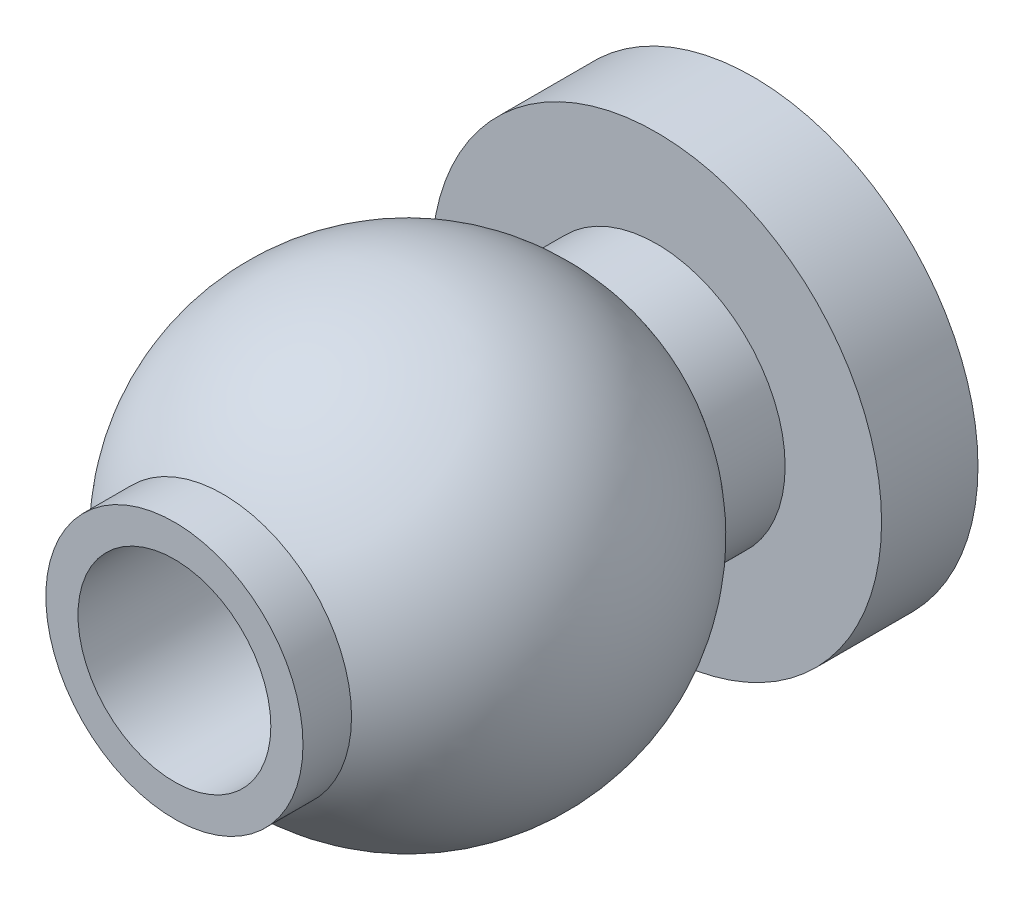
SolidWorks part; units mm, degrees
material "1060 Alloy"
ref_plane "Front Plane" through (0, 0, 0) normal (0, 0, 1) x (1, 0, 0)
ref_plane "Top Plane" through (0, 0, 0) normal (0, 1, 0) x (1, 0, 0)
ref_plane "Right Plane" through (0, 0, 0) normal (1, 0, 0) x (0, 0, -1)
sketch "Sketch1" plane through (0, 0, 0) normal (1, 0, 0) x (0, 0, -1)
  line L0 (0, 0) -> (9, 0) construction
  line L1 (0, 1.5) -> (9, 1.5)
  line L2 (9, 1.5) -> (9, 3.5)
  line L3 (9, 3.5) -> (7.5, 3.5)
  line L4 (7.5, 3.5) -> (7.5, 2)
  line L5 (7.5, 2) -> (6.5, 2)
  line L6 (0, 1.5) -> (0, 2)
  line L7 (0, 2) -> (0.7554, 2)
  arc A3 (6.5, 2) -> (0.7554, 2) centre (3.6277, 0) ccw
  dimension "D1" = 9
  dimension "D2" = 1.5
  dimension "D3" = 3.5
  dimension "D5" = 2
  dimension "D6" = 3.5
  dimension "D7" = 1.5
  dimension "D8" = 1
  dimension "D9" = 2
revolve "Revolve1" add sketch "Sketch1" angle 360 about L0
